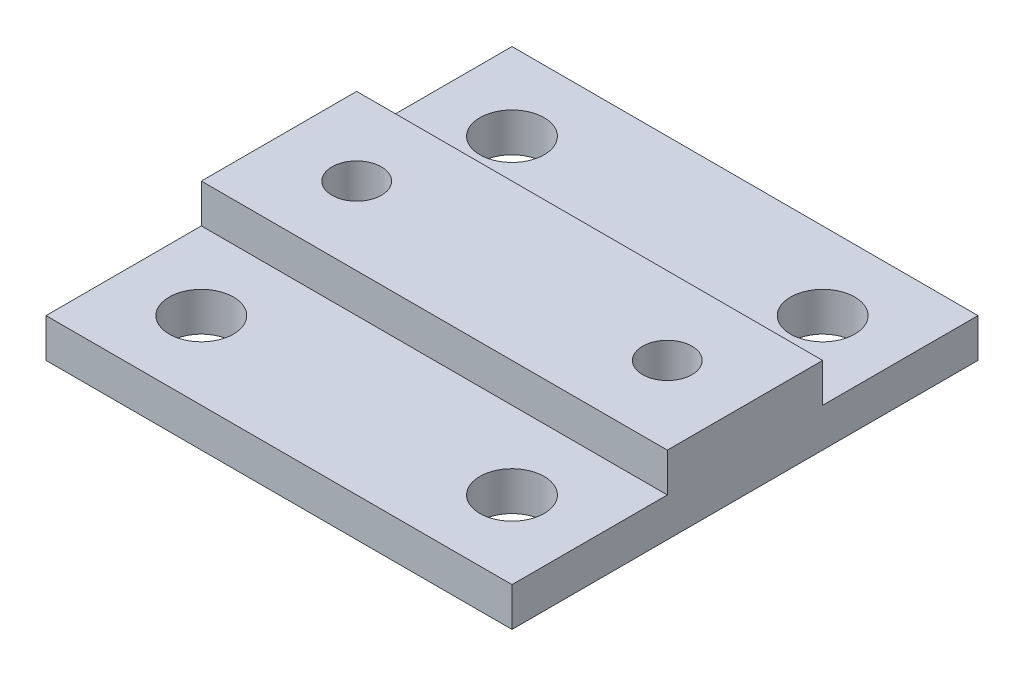
SolidWorks part; units mm, degrees
material "6061-T6 (SS)"
ref_plane "Front Plane" through (0, 0, 0) normal (0, 0, 1) x (1, 0, 0)
ref_plane "Top Plane" through (0, 0, 0) normal (0, 1, 0) x (1, 0, 0)
ref_plane "Right Plane" through (0, 0, 0) normal (1, 0, 0) x (0, 0, -1)
sketch "Sketch1" plane through (0, 0, 0) normal (0, 1, 0) x (1, 0, 0)
  line L0 (12.7, 0) -> (-12.7, 0) construction
  line L1 (0, 0) -> (0, 7.9375) construction
  line L2 (17.907, 7.9375) -> (-17.907, 7.9375) construction
  line L3 (-17.907, 7.9375) -> (-17.907, -7.9375) construction
  line L4 (-17.907, 0) -> (-12.7, 0) construction
  line L5 (17.907, -7.9375) -> (-17.907, -7.9375) construction
  line L6 (17.907, 0) -> (12.7, 0) construction
  line L7 (17.907, 7.9375) -> (17.907, -7.9375) construction
  line L8 (-12.7, 0) -> (-12.7, 12.7) construction
  line L9 (-12.7, 12.7) -> (-12.7, 19.05) construction
  line L11 (19.05, -19.05) -> (-19.05, -19.05)
  line L12 (19.05, -19.05) -> (19.05, 19.05)
  line L13 (19.05, 19.05) -> (-19.05, 19.05)
  line L14 (-19.05, -19.05) -> (-19.05, 19.05)
  line L15 (19.05, -19.05) -> (-19.05, 19.05) construction
  line L16 (19.05, 19.05) -> (-19.05, -19.05) construction
  circle A0 centre (-12.7, 0) radius 2.0193
  circle A1 centre (12.7, 0) radius 2.0193
  circle A2 centre (-12.7, 12.7) radius 2.6289
  circle A3 centre (12.7, 12.7) radius 2.6289
  circle A4 centre (12.7, -12.7) radius 2.6289
  circle A5 centre (-12.7, -12.7) radius 2.6289
  point P13 (0, -7.9375)
  dimension "D2" = 4.0386
  dimension "D6" = 5.2578
  dimension "D1" = 12.7
  dimension "D3" = 17.907
  dimension "D4" = 7.9375
  dimension "D5" = 12.7
  dimension "D7" = 6.35
  dimension "D8" = 6.35
extrude "Boss-Extrude4" add sketch "Sketch1" along normal blind 6.35
sketch "Sketch12" plane through (0, 6.35, 0) normal (0, 1, 0) x (1, 0, 0)
  line L0 (19.05, -19.05) -> (19.05, 19.05) construction
  line L1 (-19.05, 19.05) -> (19.05, 19.05)
  line L2 (-19.05, 19.05) -> (-19.05, 6.35)
  line L3 (-19.05, 6.35) -> (19.05, 6.35)
  line L4 (19.05, 19.05) -> (19.05, 6.35)
  line L5 (0, 0) -> (19.05, 0) construction
  line L6 (-19.05, -6.35) -> (19.05, -6.35)
  line L7 (19.05, -19.05) -> (19.05, -6.35)
  line L8 (-19.05, -19.05) -> (19.05, -19.05)
  line L9 (-19.05, -19.05) -> (-19.05, -6.35)
  dimension "D1" = 12.7
extrude "Cut-Extrude7" cut sketch "Sketch12" against normal blind 3.175
